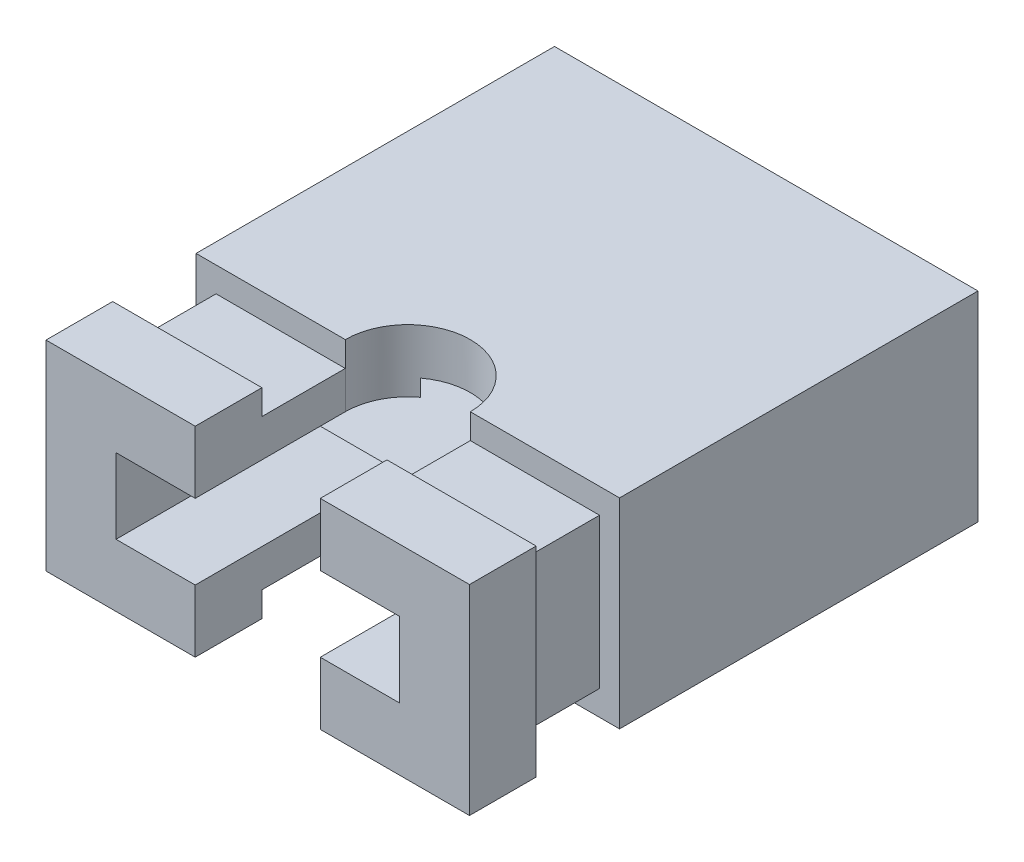
SolidWorks part; units mm, degrees
ref_plane "Front" through (0, 0, 0) normal (0, 0, 1) x (1, 0, 0)
ref_plane "Top" through (0, 0, 0) normal (0, 1, 0) x (1, 0, 0)
ref_plane "Right" through (0, 0, 0) normal (1, 0, 0) x (0, 0, -1)
sketch "Sketch1" plane through (0, 0, 0) normal (0, 0, 1) x (1, 0, 0)
  line L0 (-2.54, 1.2) -> (2.54, 1.2)
  line L1 (2.54, 1.2) -> (2.54, -1.2)
  line L2 (2.54, -1.2) -> (-2.54, -1.2)
  line L3 (-2.54, -1.2) -> (-2.54, 1.2)
extrude "Основание" add sketch "Sketch1" along normal blind 4.3
sketch "Sketch2" plane through (0, 0, 4.3) normal (0, 0, 1) x (1, 0, 0)
  line L0 (-2.3, 0.9) -> (2.3, 0.9)
  line L1 (2.3, 0.9) -> (2.3, -0.9)
  line L2 (2.3, -0.9) -> (-2.3, -0.9)
  line L3 (-2.3, -0.9) -> (-2.3, 0.9)
extrude "Паз" add sketch "Sketch2" along normal blind 1
sketch "Sketch3" plane through (0, 0, 5.3) normal (0, 0, 1) x (1, 0, 0)
  line L0 (-2.54, 1.2) -> (2.54, 1.2)
  line L1 (2.54, 1.2) -> (2.54, -1.2)
  line L2 (2.54, -1.2) -> (-2.54, -1.2)
  line L3 (-2.54, -1.2) -> (-2.54, 1.2)
extrude "Верхушка" add sketch "Sketch3" along normal blind 0.8
sketch "Sketch4" plane through (0, 0, 0) normal (0, 0, -1) x (-1, 0, 0)
  line L0 (-1.9, 0.65) -> (1.9, 0.65)
  line L1 (1.9, 0.65) -> (1.9, -0.65)
  line L2 (1.9, -0.65) -> (-1.9, -0.65)
  line L3 (-1.9, -0.65) -> (-1.9, 0.65)
extrude "Вырез большой" cut sketch "Sketch4" against normal blind 3.7
sketch "Sketch5" plane through (0, 0, 3.7) normal (0, 0, -1) x (-1, 0, 0)
  line L0 (-1.7, 0.45) -> (1.7, 0.45)
  line L1 (1.7, 0.45) -> (1.7, -0.45)
  line L2 (1.7, -0.45) -> (-1.7, -0.45)
  line L3 (-1.7, -0.45) -> (-1.7, 0.45)
extrude "Вырез маленький" cut sketch "Sketch5" against normal blind 5
sketch "Sketch7" plane through (0, -1.2, 0) normal (0, -1, 0) x (1, 0, 0)
  line L0 (-0.75, 6.1) -> (-0.75, 4.3)
  line L1 (-2.54, 6.1) -> (2.54, 6.1) construction
  line L2 (-2.54, 4.3) -> (2.54, 4.3) construction
  line L3 (-0.75, 6.1) -> (0.75, 6.1)
  line L4 (0.75, 6.1) -> (0.75, 4.3)
  arc A0 (0.75, 4.3) -> (-0.75, 4.3) centre (0, 4.3) cw
extrude "Вырез под контакт" cut sketch "Sketch7" against normal blind 3
